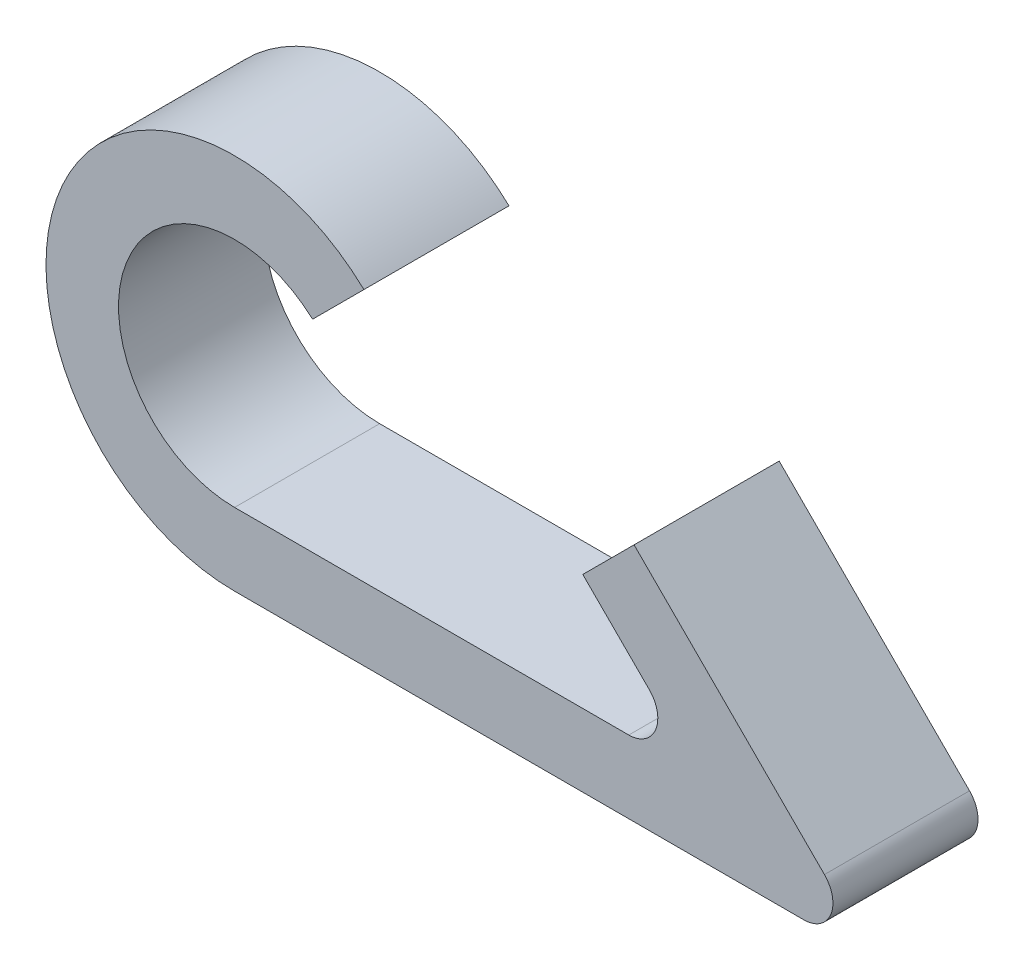
SolidWorks part; units mm, degrees
ref_plane "Plano frontal" through (0, 0, 0) normal (0, 0, 1) x (1, 0, 0)
ref_plane "Plano superior" through (0, 0, 0) normal (0, 1, 0) x (1, 0, 0)
ref_plane "Plano direito" through (0, 0, 0) normal (1, 0, 0) x (0, 0, -1)
sketch "Esboço1" plane through (0, 0, 0) normal (0, 0, 1) x (1, 0, 0)
  line L0 (0, -6.5) -> (19.6213, -6.5)
  line L1 (20.3284, -4.7929) -> (13.7678, 1.7678)
  line L2 (13.7678, 1.7678) -> (12, 0)
  line L3 (12, 0) -> (14.2929, -2.2929)
  line L4 (13.5858, -4) -> (0, -4)
  line L5 (2.6886, 2.9617) -> (4.4576, 4.7307)
  arc A0 (4.4576, 4.7307) -> (0, -6.5) centre (0, 0) ccw
  arc A1 (2.6886, 2.9617) -> (0, -4) centre (0, 0) ccw
  arc A2 (14.2929, -2.2929) -> (13.5858, -4) centre (13.5858, -3) cw
  arc A3 (19.6213, -6.5) -> (20.3284, -4.7929) centre (19.6213, -5.5) ccw
  point P12 (16, -4)
  dimension "D1" = 8
  dimension "D2" = 13
  dimension "D7" = 1
  dimension "D3" = 45
  dimension "D4" = 45
  dimension "D5" = 2.5
  dimension "D6" = 16
  dimension "D8" = 4
extrude "Ressalto-extrusão1" add sketch "Esboço1" along normal blind 5
